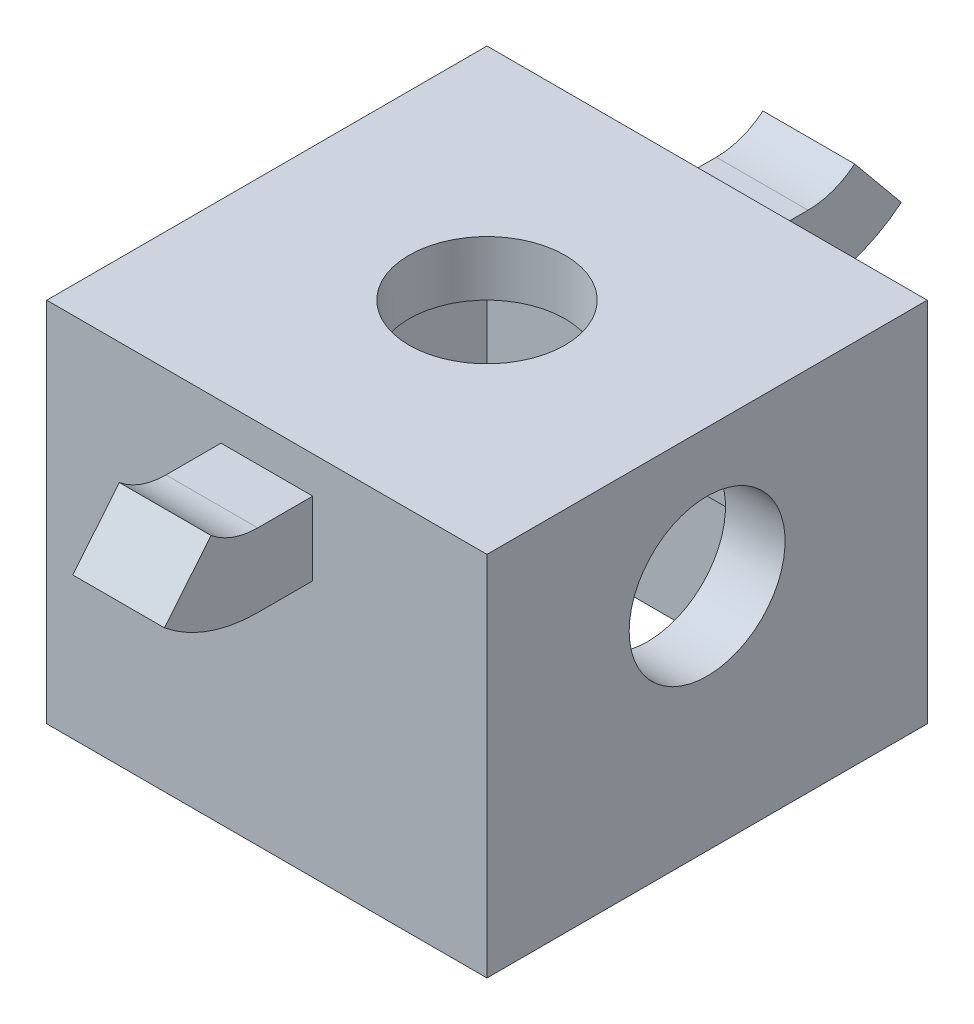
SolidWorks part; units mm, degrees
ref_plane "Front Plane" through (0, 0, 0) normal (0, 0, 1) x (1, 0, 0)
ref_plane "Top Plane" through (0, 0, 0) normal (0, 1, 0) x (1, 0, 0)
ref_plane "Right Plane" through (0, 0, 0) normal (1, 0, 0) x (0, 0, -1)
sketch "Sketch1" plane through (0, 0, 0) normal (0, 1, 0) x (1, 0, 0)
  line L1 (12, -12) -> (-12, -12)
  line L2 (12, -12) -> (12, 12)
  line L3 (12, 12) -> (-12, 12)
  line L4 (-12, -12) -> (-12, 12)
  line L5 (12, -12) -> (-12, 12) construction
  line L6 (12, 12) -> (-12, -12) construction
  point P0 (0, 0)
  dimension "D1" = 24
extrude "Boss-Extrude1" add sketch "Sketch1" along normal blind 20
sketch "Sketch3" plane through (0, 0, 0) normal (0, -1, 0) x (1, 0, 0)
  line L0 (12, -12) -> (-12, -12) construction
  line L1 (-10, -10) -> (10, -10)
  line L2 (-10, -10) -> (-10, 10)
  line L3 (-10, 10) -> (10, 10)
  line L4 (10, -10) -> (10, 10)
  line L5 (-10, -10) -> (10, 10) construction
  line L6 (-10, 10) -> (10, -10) construction
  point P0 (0, 0)
  dimension "D1" = 2
sketch "Sketch5" plane through (0, 0, -12) normal (0, 0, -1) x (-1, 0, 0)
  line L0 (-12, 0) -> (12, 20) construction
  line L1 (-12, 20) -> (12, 0) construction
  line L2 (0, 16) -> (0, 10) construction
  line L3 (2.5, 18) -> (-2.5, 18)
  line L4 (2.5, 18) -> (2.5, 14)
  line L5 (2.5, 14) -> (-2.5, 14)
  line L6 (-2.5, 18) -> (-2.5, 14)
  line L7 (2.5, 18) -> (-2.5, 14) construction
  line L8 (2.5, 14) -> (-2.5, 18) construction
  dimension "D1" = 5
  dimension "D2" = 4
  dimension "D3" = 6
sketch "Sketch6" plane through (0, 0, 0) normal (1, 0, 0) x (0, 0, -1)
  line L0 (12, 16) -> (15, 16)
  arc A0 (15, 16) -> (18.8134, 17.3677) centre (15, 22) ccw
  dimension "D2" = 6
  dimension "D1" = 3
sweep "Sweep1" add profiles "Sketch5" path "Sketch6"
mirror "Mirror1" about plane through (0, 0, 0) normal (0, 0, 1) of "Sweep1"
extrude "Cut-Extrude5" cut sketch "Sketch3" against normal blind 6
sketch "Sketch14" plane through (0, 6, 0) normal (0, -1, 0) x (1, 0, 0)
  line L1 (10, 10) -> (-10, 10)
  line L2 (10, 10) -> (10, -10)
  line L3 (10, -10) -> (-10, -10)
  line L4 (-10, 10) -> (-10, -10)
  line L5 (10, 10) -> (-10, -10) construction
  line L6 (10, -10) -> (-10, 10) construction
  point P0 (0, 0)
extrude "Cut-Extrude6" cut sketch "Sketch14" against normal blind 2
sketch "Sketch15" plane through (0, 8, 0) normal (0, -1, 0) x (1, 0, 0)
  line L1 (8.75, -8.75) -> (-8.75, -8.75)
  line L2 (8.75, -8.75) -> (8.75, 8.75)
  line L3 (8.75, 8.75) -> (-8.75, 8.75)
  line L4 (-8.75, -8.75) -> (-8.75, 8.75)
  line L5 (8.75, -8.75) -> (-8.75, 8.75) construction
  line L6 (8.75, 8.75) -> (-8.75, -8.75) construction
  line L7 (10, 10) -> (-10, 10) construction
  point P0 (0, 0)
  dimension "D1" = 1.25
extrude "Cut-Extrude7" cut sketch "Sketch15" against normal blind 9
sketch "Sketch16" plane through (0, 17, 0) normal (0, -1, 0) x (1, 0, 0)
  circle A0 centre (0, 0) radius 4.25
  dimension "D1" = 8.5
extrude "Cut-Extrude8" cut sketch "Sketch16" against normal up to next
sketch "Sketch17" plane through (8.75, 0, 0) normal (-1, 0, 0) x (0, 0, 1)
  line L0 (8.75, 17) -> (-8.75, 8) construction
  circle A0 centre (0, 12.5) radius 4.25
  dimension "D1" = 8.5
extrude "Cut-Extrude9" cut sketch "Sketch17" against normal up to next
